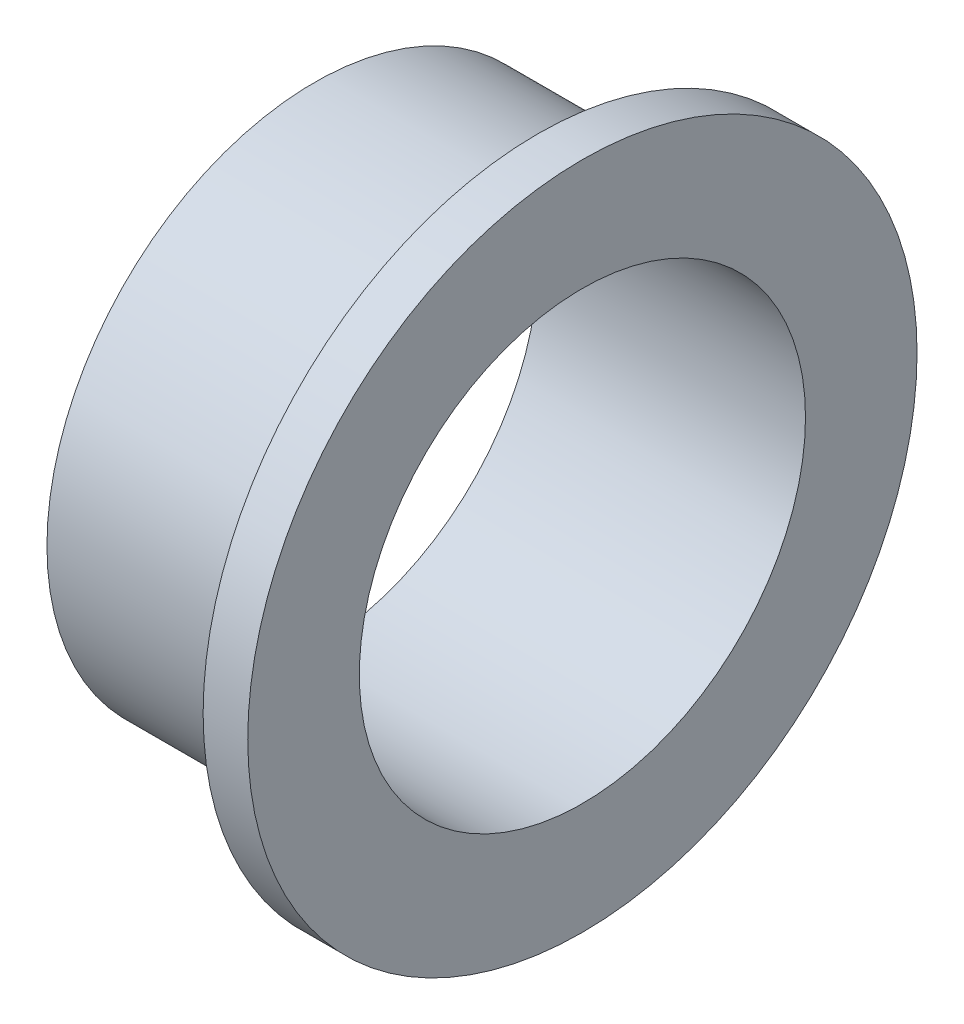
SolidWorks part; units mm, degrees
material "2014-T6"
ref_plane "Ebene vorne" through (0, 0, 0) normal (0, 0, 1) x (1, 0, 0)
ref_plane "Ebene oben" through (0, 0, 0) normal (0, 1, 0) x (1, 0, 0)
ref_plane "Ebene rechts" through (0, 0, 0) normal (1, 0, 0) x (0, 0, -1)
sketch "Skizze1" plane through (0, 0, 0) normal (0, 0, 1) x (1, 0, 0)
  line L0 (-6, 5) -> (0, 5)
  line L1 (0, 5) -> (0, 7.5)
  line L2 (0, 7.5) -> (-1, 7.5)
  line L3 (-1, 7.5) -> (-1, 6)
  line L4 (-1, 6) -> (-6, 6)
  line L5 (-6, 6) -> (-6, 5)
  line L6 (0, 5) -> (0, 0) construction
  line L7 (-6.6765, 0) -> (-51.0928, 0) construction
  dimension "D1" = 10
  dimension "D2" = 12
  dimension "D3" = 5
  dimension "D4" = 1
  dimension "D5" = 15
revolve "Rotation1" add sketch "Skizze1" angle 360 about L7
